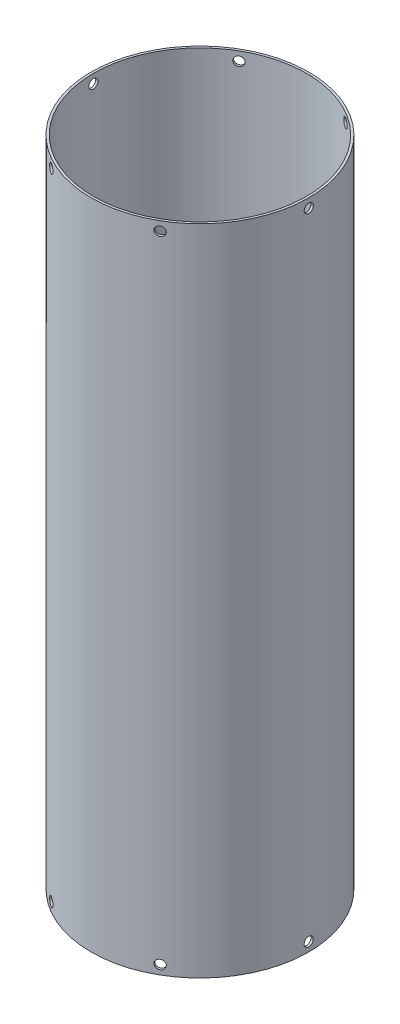
SolidWorks part; units mm, degrees
material "Hexcel AS4C (3000 Filaments)"
ref_plane "Front Plane" through (0, 0, 0) normal (0, 0, 1) x (1, 0, 0)
ref_plane "Top Plane" through (0, 0, 0) normal (0, 1, 0) x (1, 0, 0)
ref_plane "Right Plane" through (0, 0, 0) normal (1, 0, 0) x (0, 0, -1)
sketch "Sketch1" plane through (0, 0, 0) normal (0, 1, 0) x (1, 0, 0)
  circle A0 centre (0, 0) radius 152.4
  circle A1 centre (0, 0) radius 149.225
  dimension "D2" = 304.8
  dimension "D1" = 3.175
extrude "Boss-Extrude1" add sketch "Sketch1" along normal blind 914.4
ref_plane "Plane1" through (-152.4, 0, 0) normal (-1, 0, 0) x (0, 0, 1)
hole_wizard "1/2 (0.5) Diameter Hole1" positions "Sketch2" profile "Sketch3" hole size "1/2" standard "ANSI Inch"
sketch "Sketch2" plane through (-152.4, 0, 0) normal (-1, 0, 0) x (0, 0, 1)
  line L0 (0, -167.64) -> (0, 167.64) construction
  line L1 (152.4, 914.4) -> (-152.4, 914.4) construction
  point P0 (0, 901.7)
  dimension "D1" = 12.7
sketch "Sketch3" plane through (-152.4, 901.7, 0) normal (0, 1, 0) x (0, 0, 1)
  line L0 (0, 0) -> (0, 356.2465)
  line L1 (0, 356.2465) -> (6.35, 356.2465)
  line L2 (6.35, 356.2465) -> (6.35, 0)
  line L5 (6.35, 0) -> (0, 0)
  line L11 (0, -6.35) -> (0, 107.95) construction
  dimension "Thru Hole Dia." = 12.7
  dimension "Thru Hole Depth" = 356.2465
pattern_circular "CirPattern1" count 6 over 360 about axis through (0, 914.4, 0) along (0, 1, 0) of "1/2 (0.5) Diameter Hole1"
ref_plane "Plane2" through (0, 457.2, 0) normal (0, 1, 0) x (1, 0, 0)
mirror "Mirror1" about plane through (0, 457.2, 0) normal (0, 1, 0) of "CirPattern1", "1/2 (0.5) Diameter Hole1"
